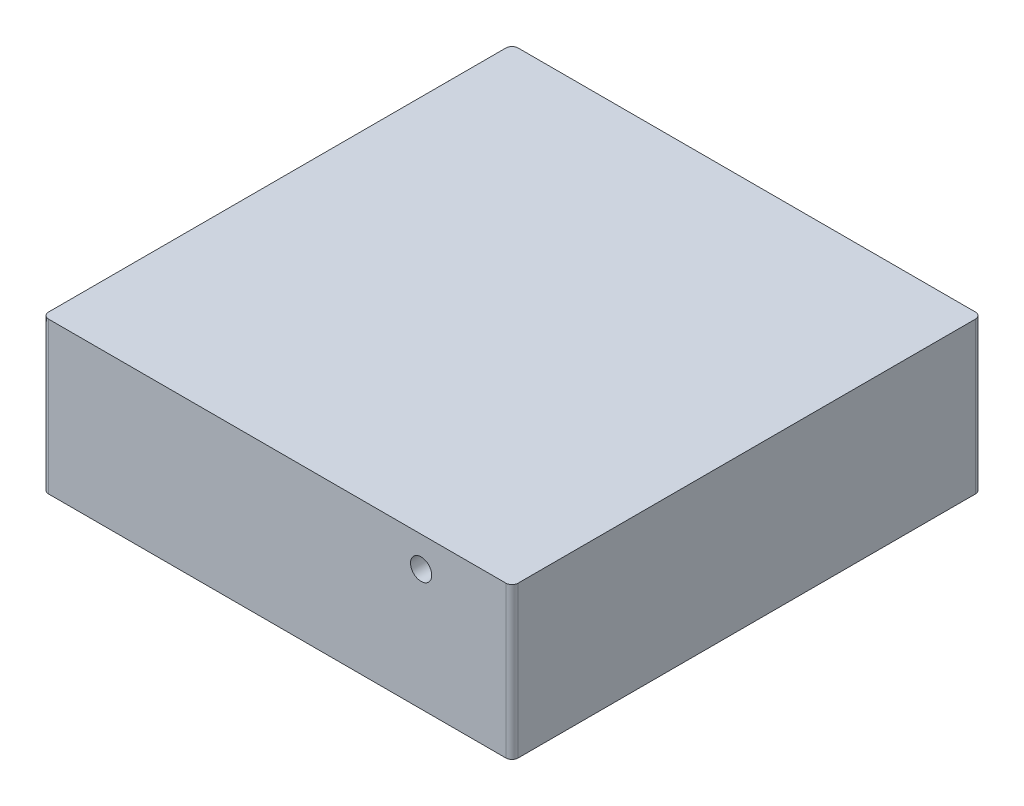
SolidWorks part; units mm, degrees
ref_plane "Front" through (0, 0, 0) normal (0, 0, 1) x (1, 0, 0)
ref_plane "Top" through (0, 0, 0) normal (0, 1, 0) x (1, 0, 0)
ref_plane "Right" through (0, 0, 0) normal (1, 0, 0) x (0, 0, -1)
sketch "Sketch1" plane through (0, 0, 0) normal (0, 1, 0) x (1, 0, 0)
  line L1 (0, 0) -> (77.5, 0)
  line L2 (0, 0) -> (0, 77.5)
  line L3 (0, 77.5) -> (77.5, 77.5)
  line L4 (77.5, 0) -> (77.5, 77.5)
  dimension "D1" = 77.5
  dimension "D2" = 77.5
extrude "Boss-Extrude1" add sketch "Sketch1" along normal blind 25
sketch "Sketch2" plane through (0, 0, 0) normal (0, 1, 0) x (1, 0, 0)
  line L1 (3.5, 3.5) -> (74, 3.5)
  line L2 (3.5, 3.5) -> (3.5, 74)
  line L3 (3.5, 74) -> (74, 74)
  line L4 (74, 3.5) -> (74, 74)
  line L5 (77.5, 77.5) -> (0, 77.5) construction
  line L7 (0, 77.5) -> (0, 0) construction
  dimension "D1" = 70.5
  dimension "D2" = 70.5
  dimension "D3" = 3.5
  dimension "D4" = 3.5
extrude "Cut-Extrude1" cut sketch "Sketch2" along normal blind 23
sketch "Sketch4" plane through (0, 0, 0) normal (0, 1, 0) x (1, 0, 0)
  line L0 (0, 0) -> (77.5, 0) construction
  line L1 (1, 1) -> (76.5, 1)
  line L2 (1, 1) -> (1, 76.5)
  line L3 (1, 76.5) -> (76.5, 76.5)
  line L4 (76.5, 1) -> (76.5, 76.5)
  line L5 (2.5, 2.5) -> (75, 2.5)
  line L6 (2.5, 2.5) -> (2.5, 75)
  line L7 (2.5, 75) -> (75, 75)
  line L8 (75, 2.5) -> (75, 75)
  line L9 (0, 77.5) -> (0, 0) construction
  line L10 (3.5, 3.5) -> (74, 3.5) construction
  line L13 (74, 74) -> (3.5, 74) construction
  line L16 (3.5, 74) -> (3.5, 3.5) construction
  line L18 (77.5, 0) -> (77.5, 77.5) construction
  dimension "D1" = 1
  dimension "D2" = 1
  dimension "D3" = 1
  dimension "D4" = 1
  dimension "D5" = 1.5
  dimension "D6" = 1
  dimension "D7" = 1
extrude "Cut-Extrude3" cut sketch "Sketch4" along normal blind 4
sketch "Sketch5" plane through (0, 0, 0) normal (0, 1, 0) x (1, 0, 0)
  line L0 (3.5, 3.5) -> (74, 3.5) construction
  line L1 (3.5, 74) -> (3.5, 3.5) construction
  line L2 (74, 3.5) -> (74, 74) construction
  line L3 (3.5, 3.5) -> (74, 3.5) construction
  line L4 (74, 74) -> (3.5, 74) construction
  circle A0 centre (10.5, 10.5) radius 1
  circle A1 centre (67, 10.5) radius 1
  circle A2 centre (67, 67) radius 1
  circle A3 centre (10.5, 67) radius 1
  dimension "D1" = 2
  dimension "D2" = 2
  dimension "D3" = 2
  dimension "D4" = 2
  dimension "D5" = 7
  dimension "D6" = 7
  dimension "D7" = 7
  dimension "D8" = 7
  dimension "D9" = 7
  dimension "D10" = 7
  dimension "D11" = 7
  dimension "D12" = 7
extrude "Boss-Extrude2" add sketch "Sketch5" along normal blind 21 from offset 2 separate body
sketch "Sketch6" plane through (0, 0, 0) normal (0, 0, 1) x (1, 0, 0)
  line L0 (77.5, 25) -> (77.5, 0) construction
  line L1 (0, 25) -> (77.5, 25) construction
  circle A0 centre (62.5, 20) radius 1.75
  dimension "D1" = 3.5
  dimension "D2" = 15
  dimension "D3" = 5
extrude "Cut-Extrude4" cut sketch "Sketch6" against normal blind 7
sketch "Sketch7" plane through (0, 0, 0) normal (1, 0, 0) x (0, 0, -1)
  line L0 (77.5, 25) -> (0, 25) construction
  line L1 (77.5, 25) -> (77.5, 0) construction
  circle A0 centre (62.5, 20) radius 2
  dimension "D1" = 5
  dimension "D2" = 15
  dimension "D3" = 4
extrude "Cut-Extrude6" cut sketch "Sketch7" along normal blind 3.5
fillet "Fillet6" radius 1 1 edges at (77.5, 12.5, -77.5)
fillet "Fillet7" radius 1 1 edges at (77.5, 12.5, 0)
fillet "Fillet8" radius 1 1 edges at (0, 12.5, 0)
fillet "Fillet9" radius 1 1 edges at (0, 12.5, -77.5)
